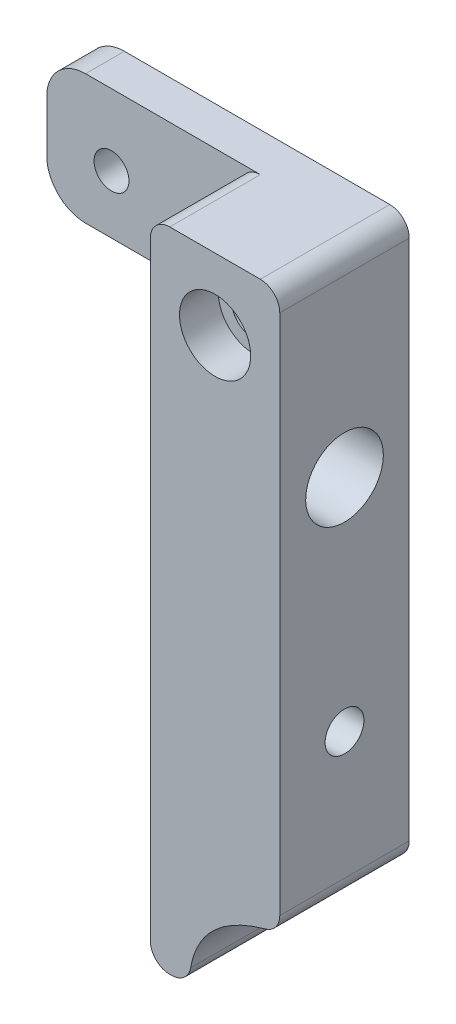
SolidWorks part; units mm, degrees
ref_plane "Front Plane" through (0, 0, 0) normal (0, 0, 1) x (1, 0, 0)
ref_plane "Top Plane" through (0, 0, 0) normal (0, 1, 0) x (1, 0, 0)
ref_plane "Right Plane" through (0, 0, 0) normal (1, 0, 0) x (0, 0, -1)
sketch "Sketch1" plane through (0, 0, 0) normal (0, 0, 1) x (1, 0, 0)
  line L1 (-5, 25) -> (5, 25)
  line L2 (-5, 25) -> (-5, -25)
  line L3 (-5, -25) -> (5, -25)
  line L4 (5, 25) -> (5, -25)
  line L5 (-5, 25) -> (5, -25) construction
  line L6 (-5, -25) -> (5, 25) construction
  point P0 (0, 0)
  dimension "D1" = 10
  dimension "D2" = 50
extrude "Boss-Extrude1" add sketch "Sketch1" along normal blind 10
sketch "Sketch2" plane through (0, 0, 10) normal (0, 0, 1) x (1, 0, 0)
  line L0 (5, 25) -> (-5, 25) construction
  circle A0 centre (0, 19.5) radius 1.75
  dimension "D1" = 3.5
  dimension "D2" = 5.5
extrude "Cut-Extrude1" cut sketch "Sketch2" against normal blind 10
sketch "Sketch3" plane through (0, 0, 10) normal (0, 0, 1) x (1, 0, 0)
  line L0 (5, -18) -> (5, -25)
  line L1 (5, -25) -> (5, 25) construction
  line L2 (5, -25) -> (-2, -25)
  line L3 (-5, -25) -> (5, -25) construction
  spline S0 degree 2 poles (-2, -25) (-1.9042, -19.4309) (5, -18) knots 0 0 0 1 1 1
  dimension "D1" = 7
  dimension "D2" = 7
  dimension "D3" = 7
extrude "Cut-Extrude2" cut sketch "Sketch3" against normal blind 10
fillet "Fillet1" radius 1.5 4 edges at (5, -18, 5) (-2, -25, 5) (-5, -25, 5) (5, 25, 5)
sketch "Sketch4" plane through (0, 0, 10) normal (0, 0, 1) x (1, 0, 0)
  circle A0 centre (0, 19.5) radius 2.75
  dimension "D1" = 5.5
extrude "Cut-Extrude3" cut sketch "Sketch4" against normal blind 3
sketch "Sketch5" plane through (5, 0, 0) normal (1, 0, 0) x (0, 0, -1)
  line L0 (-10, 25) -> (0, 25) construction
  line L1 (0, -16.8206) -> (0, 23.5) construction
  circle A0 centre (-5, 10) radius 3
  dimension "D2" = 6
  dimension "D1" = 15
  dimension "D3" = 5
extrude "Cut-Extrude4" cut sketch "Sketch5" against normal blind 13
sketch "Sketch6" plane through (-5, 0, 0) normal (-1, 0, 0) x (0, 0, 1)
  line L1 (0, 25) -> (3, 25)
  line L2 (0, 25) -> (0, 15)
  line L3 (0, 15) -> (3, 15)
  line L4 (3, 25) -> (3, 15)
  dimension "D1" = 10
  dimension "D2" = 3
extrude "Boss-Extrude2" add sketch "Sketch6" along normal blind 15
fillet "Fillet2" radius 3 2 edges at (-20, 25, 1.5) (-20, 15, 1.5)
fillet "Fillet3" radius 1.5 1 edges at (-5, 25, 6.5)
sketch "Sketch7" plane through (0, 0, 3) normal (0, 0, 1) x (1, 0, 0)
  line L0 (-5, 23.5) -> (-5, -23.5) construction
  line L1 (-17, 25) -> (-3.5, 25) construction
  circle A0 centre (-15, 19.5) radius 1.35
  dimension "D1" = 2.7
  dimension "D2" = 10
  dimension "D3" = 5.5
extrude "Cut-Extrude5" cut sketch "Sketch7" against normal blind 15
sketch "Sketch8" plane through (5, 0, 0) normal (1, 0, 0) x (0, 0, -1)
  line L1 (-10, 25) -> (0, 25) construction
  line L2 (0, -16.8206) -> (0, 23.5) construction
  circle A0 centre (-5, -7) radius 1.5
  dimension "D3" = 3
  dimension "D1" = 32
  dimension "D2" = 5
extrude "Cut-Extrude6" cut sketch "Sketch8" against normal blind 15
